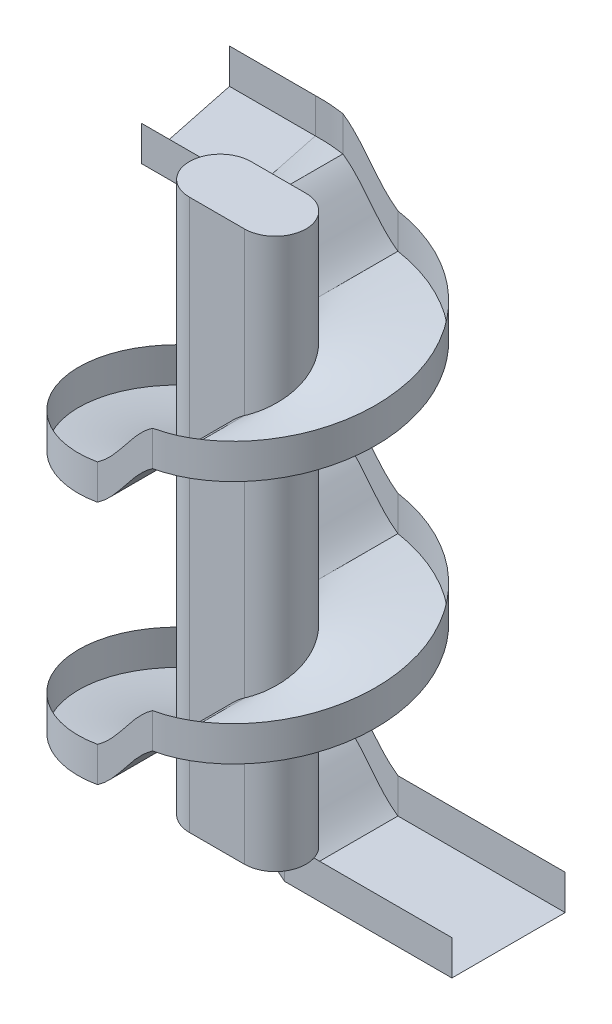
SolidWorks part; units mm, degrees
ref_plane "Front Plane" through (0, 0, 0) normal (0, 0, 1) x (1, 0, 0)
ref_plane "Top Plane" through (0, 0, 0) normal (0, 1, 0) x (1, 0, 0)
ref_plane "Right Plane" through (0, 0, 0) normal (1, 0, 0) x (0, 0, -1)
sketch "Sketch1" plane through (0, 0, 0) normal (0, 1, 0) x (1, 0, 0)
  line L0 (125, 0) -> (-125, 0) construction
  line L1 (125, -140) -> (-125, -140)
  line L2 (125, 140) -> (-125, 140)
  arc A0 (125, -140) -> (125, 140) centre (125, 0) ccw
  arc A1 (-125, 140) -> (-125, -140) centre (-125, 0) ccw
  point P2 (0, 0)
  dimension "D2" = 140
  dimension "D1" = 250
extrude "Boss-Extrude1" add sketch "Sketch1" along normal blind 2500
sketch "Sketch2" plane through (0, 0, 0) normal (0, 1, 0) x (1, 0, 0)
  line L0 (0, 0) -> (207.5125, 232.4141)
  point P3 (125, 140)
sketch "Sketch3" plane through (0, 0, 0) normal (0, 0, 1) x (1, 0, 0)
  line L0 (0, 0) -> (0, 2500)
  line L1 (-125, 2500) -> (125, 2500) construction
surface "Surface-Sweep1" parameters "D0"=810
sketch3d "3DSketch1"
  spline S2 degree 3 poles (215.4149, 2255.487, -593.0677) (166.0359, 1865.4917, -34.2644) (-1.7183, 1753.0109, 152.723) (-143.1351, 1653.9689, 138.8944) (-147.6117, 1650.8283, 138.2359) (-156.4867, 1644.5664, 136.4882) (-160.8853, 1641.4451, 135.3991) (-169.592, 1635.2055, 132.7863) (-173.9017, 1632.0894, 131.262) (-179.2125, 1628.1692, 129.0826) (-180.271, 1627.3841, 128.633) (-182.3803, 1625.8114, 127.706) (-183.4301, 1625.0246, 127.2291) (-186.5537, 1622.6708, 125.7634) (-188.6059, 1621.1073, 124.7378) (-194.6711, 1616.4304, 121.5191) (-198.593, 1613.3309, 119.184) (-206.1879, 1607.1521, 114.1459) (-209.8612, 1604.0737, 111.4426) (-216.9467, 1597.919, 105.6725) (-220.3543, 1594.8339, 102.6096) (-225.2526, 1590.1828, 97.7482) (-226.8498, 1588.6284, 96.0831) (-229.9709, 1585.5098, 92.6632) (-231.4853, 1583.9547, 90.9185) (-235.8841, 1579.3068, 85.5917) (-238.6272, 1576.2278, 81.9134) (-243.7356, 1570.0929, 74.3157) (-246.1013, 1567.0395, 70.3947) (-250.4404, 1560.9151, 62.3349) (-252.4149, 1557.8468, 58.1948) (-255.0755, 1553.2232, 51.8234) (-255.9121, 1551.6785, 49.6727) (-257.09, 1549.3547, 46.4066) (-257.4702, 1548.578, 45.3099) (-258.2023, 1547.027, 43.1101) (-258.5541, 1546.253, 42.0075) (-260.2425, 1542.3895, 36.4808) (-261.3671, 1539.3199, 32.0168) (-263.1715, 1533.2068, 23.0154) (-263.85, 1530.1546, 18.4837) (-264.761, 1524.0396, 9.3717) (-264.9936, 1520.9776, 4.7909) (-265.003, 1516.3659, -2.1103) (-264.9227, 1514.0555, -5.5684) (-264.7129, 1511.7358, -9.0364) (-264.5439, 1510.187, -11.3505) (-264.445, 1509.4119, -12.5078) (-263.8798, 1505.548, -18.2726) (-263.2012, 1502.4828, -22.8368) (-261.4079, 1496.3583, -31.843) (-260.2933, 1493.3005, -36.286) (-257.635, 1487.1786, -45.0432) (-256.0914, 1484.1145, -49.3574) (-253.4529, 1479.502, -55.7236) (-252.0528, 1477.1917, -58.8804) (-250.5303, 1474.873, -61.9959) (-249.4879, 1473.3251, -64.0634) (-248.9523, 1472.5492, -65.0935) (-246.2137, 1468.6752, -70.2051) (-243.8354, 1465.5946, -74.1565) (-238.7265, 1459.4405, -81.7761) (-235.9952, 1456.3692, -85.4455) (-230.1896, 1450.2225, -92.4987) (-227.1152, 1447.1472, -95.8826) (-222.2492, 1442.5197, -100.7365) (-220.5848, 1440.9748, -102.3174) (-217.1708, 1437.878, -105.4032) (-215.4213, 1436.3261, -106.9081) (-212.7356, 1433.9864, -109.1045) (-211.8308, 1433.2053, -109.8259) (-210.0089, 1431.6465, -111.2422) (-207.2547, 1429.3106, -113.3288) (-204.4379, 1426.9806, -115.3033) (-198.7238, 1422.3254, -119.1038) (-194.8073, 1419.2283, -121.4399) (-186.7723, 1413.0313, -125.7175) (-182.6539, 1409.9313, -127.659) (-176.3314, 1405.2672, -130.2701) (-174.1997, 1403.7102, -131.0901) (-169.8932, 1400.5825, -132.6267) (-167.7179, 1399.0126, -133.3433) (-164.4225, 1396.6471, -134.3398) (-163.3177, 1395.8562, -134.6591) (-161.1023, 1394.2739, -135.2699) (-157.7726, 1391.9015, -136.1439) (-154.4242, 1389.531, -136.892) (-147.7049, 1384.7891, -138.2221) (-143.1955, 1381.6269, -138.8873) (-10.2284, 1288.5955, -151.9254) (139.3738, 1193.9891, 12.7072) (-68.7291, 543.0017, 420.957) knots -0.917382 -0.917382 -0.917382 -0.917382 0.03125 0.03125 0.0625 0.0625 0.09375 0.09375 0.125 0.125 0.132813 0.132813 0.140625 0.140625 0.15625 0.15625 0.1875 0.1875 0.21875 0.21875 0.25 0.25 0.265625 0.265625 0.28125 0.28125 0.3125 0.3125 0.34375 0.34375 0.375 0.375 0.390625 0.390625 0.398438 0.398438 0.40625 0.40625 0.4375 0.4375 0.46875 0.46875 0.5 0.5 0.515625 0.523438 0.523438 0.53125 0.53125 0.5625 0.5625 0.59375 0.59375 0.625 0.625 0.640625 0.648438 0.648438 0.65625 0.65625 0.6875 0.6875 0.71875 0.71875 0.75 0.75 0.765625 0.765625 0.78125 0.78125 0.789063 0.789063 0.796875 0.8125 0.8125 0.84375 0.84375 0.875 0.875 0.890625 0.890625 0.90625 0.90625 0.914063 0.914063 0.921875 0.9375 0.9375 0.96875 0.96875 1.854106 1.854106 1.854106 1.854106 only from (-125, 1666.6667, 140) to (-125, 1368.8979, -140)
  spline S3 degree 3 poles (215.4149, 1144.3759, -593.0677) (166.0359, 754.3806, -34.2644) (-1.7183, 641.8998, 152.723) (-143.1351, 542.8578, 138.8944) (-147.6117, 539.7172, 138.2359) (-156.4867, 533.4553, 136.4882) (-160.8853, 530.334, 135.3991) (-169.592, 524.0944, 132.7863) (-173.9017, 520.9783, 131.262) (-179.2125, 517.0581, 129.0826) (-180.271, 516.273, 128.633) (-182.3803, 514.7003, 127.706) (-183.4301, 513.9134, 127.2291) (-186.5537, 511.5597, 125.7634) (-188.6059, 509.9961, 124.7378) (-194.6711, 505.3193, 121.5191) (-198.593, 502.2198, 119.184) (-206.1879, 496.041, 114.1459) (-209.8612, 492.9626, 111.4426) (-216.9467, 486.8079, 105.6725) (-220.3543, 483.7228, 102.6096) (-225.2526, 479.0716, 97.7482) (-226.8498, 477.5173, 96.0831) (-229.9709, 474.3987, 92.6632) (-231.4853, 472.8436, 90.9185) (-235.8841, 468.1957, 85.5917) (-238.6272, 465.1167, 81.9134) (-243.7356, 458.9818, 74.3157) (-246.1013, 455.9284, 70.3947) (-250.4404, 449.804, 62.3349) (-252.4149, 446.7357, 58.1948) (-255.0755, 442.1121, 51.8234) (-255.9121, 440.5674, 49.6727) (-257.09, 438.2436, 46.4066) (-257.4702, 437.4669, 45.3099) (-258.2023, 435.9159, 43.1101) (-258.5541, 435.1419, 42.0075) (-260.2425, 431.2784, 36.4808) (-261.3671, 428.2088, 32.0168) (-263.1715, 422.0957, 23.0154) (-263.85, 419.0435, 18.4837) (-264.761, 412.9285, 9.3717) (-264.9936, 409.8665, 4.7909) (-265.003, 405.2548, -2.1103) (-264.9227, 402.9444, -5.5684) (-264.7129, 400.6247, -9.0364) (-264.5439, 399.0759, -11.3505) (-264.445, 398.3008, -12.5078) (-263.8798, 394.4369, -18.2726) (-263.2012, 391.3717, -22.8368) (-261.4079, 385.2472, -31.843) (-260.2933, 382.1894, -36.286) (-257.635, 376.0674, -45.0432) (-256.0914, 373.0033, -49.3574) (-253.4529, 368.3909, -55.7236) (-252.0528, 366.0806, -58.8804) (-250.5303, 363.7619, -61.9959) (-249.4879, 362.214, -64.0634) (-248.9523, 361.4381, -65.0935) (-246.2137, 357.5641, -70.2051) (-243.8354, 354.4835, -74.1565) (-238.7265, 348.3294, -81.7761) (-235.9952, 345.258, -85.4455) (-230.1896, 339.1114, -92.4987) (-227.1152, 336.0361, -95.8826) (-222.2492, 331.4086, -100.7365) (-220.5848, 329.8637, -102.3174) (-217.1708, 326.7669, -105.4032) (-215.4213, 325.215, -106.9081) (-212.7356, 322.8753, -109.1045) (-211.8308, 322.0942, -109.8259) (-210.0089, 320.5354, -111.2422) (-207.2547, 318.1995, -113.3288) (-204.4379, 315.8695, -115.3033) (-198.7238, 311.2143, -119.1038) (-194.8073, 308.1172, -121.4399) (-186.7723, 301.9202, -125.7175) (-182.6539, 298.8202, -127.659) (-176.3314, 294.1561, -130.2701) (-174.1997, 292.5991, -131.0901) (-169.8932, 289.4714, -132.6267) (-167.7179, 287.9015, -133.3433) (-164.4225, 285.536, -134.3398) (-163.3177, 284.7451, -134.6591) (-161.1023, 283.1628, -135.2699) (-157.7726, 280.7904, -136.1439) (-154.4242, 278.4199, -136.892) (-147.7049, 273.678, -138.2221) (-143.1955, 270.5157, -138.8873) (-10.2284, 177.4843, -151.9254) (139.3738, 82.878, 12.7072) (-68.7291, -568.1094, 420.957) knots -0.917382 -0.917382 -0.917382 -0.917382 0.03125 0.03125 0.0625 0.0625 0.09375 0.09375 0.125 0.125 0.132813 0.132813 0.140625 0.140625 0.15625 0.15625 0.1875 0.1875 0.21875 0.21875 0.25 0.25 0.265625 0.265625 0.28125 0.28125 0.3125 0.3125 0.34375 0.34375 0.375 0.375 0.390625 0.390625 0.398438 0.398438 0.40625 0.40625 0.4375 0.4375 0.46875 0.46875 0.5 0.5 0.515625 0.523438 0.523438 0.53125 0.53125 0.5625 0.5625 0.59375 0.59375 0.625 0.625 0.640625 0.648438 0.648438 0.65625 0.65625 0.6875 0.6875 0.71875 0.71875 0.75 0.75 0.765625 0.765625 0.78125 0.78125 0.789063 0.789063 0.796875 0.8125 0.8125 0.84375 0.84375 0.875 0.875 0.890625 0.890625 0.90625 0.90625 0.914063 0.914063 0.921875 0.9375 0.9375 0.96875 0.96875 1.854106 1.854106 1.854106 1.854106 only from (-125, 555.5556, 140) to (-125, 257.7868, -140)
  spline S4 degree 3 poles (-167.7542, 1598.7248, 330.6483) (117.7392, 2309.6969, 1.7989) (-12.367, 2401.3101, -145.9603) (-134.5575, 2486.6957, -139.6938) (-136.9403, 2488.3611, -139.5104) (-284.7397, 2591.7937, -124.3152) (-410.6575, 2687.9461, 118.4195) (-310.3715, 3060.5098, 676.0833) knots -12.296716 -12.296716 -12.296716 -12.296716 0.25 0.25 0.5 0.5 15.791017 15.791017 15.791017 15.791017 only from (-125, 2480.009, -140) to (-153.5135, 2500, -137.0656)
  spline S5 degree 3 poles (-125, 2480.009, -140) (-127.392, 2481.6883, -140) (-129.7832, 2483.3595, -139.9387) (-134.5575, 2486.6957, -139.6938) (-136.9403, 2488.3611, -139.5104) (-144.073, 2493.3527, -138.7771) (-148.8073, 2496.6744, -138.0446) (-153.5135, 2500, -137.0656) knots 0 0 0 0 0.25 0.25 0.5 0.5 1 1 1 1
  spline S6 degree 3 poles (-125, 555.5556, 140) (-129.5716, 552.3516, 140) (-134.1151, 549.175, 139.7764) (-143.1351, 542.8578, 138.8944) (-147.6117, 539.7172, 138.2359) (-156.4867, 533.4553, 136.4882) (-160.8853, 530.334, 135.3991) (-169.592, 524.0944, 132.7863) (-173.9017, 520.9783, 131.262) (-179.2125, 517.0581, 129.0826) (-180.271, 516.273, 128.633) (-182.3803, 514.7003, 127.706) (-183.4301, 513.9134, 127.2291) (-186.5537, 511.5597, 125.7634) (-188.6059, 509.9961, 124.7378) (-194.6711, 505.3193, 121.5191) (-198.593, 502.2198, 119.184) (-206.1879, 496.041, 114.1459) (-209.8612, 492.9626, 111.4426) (-216.9467, 486.8079, 105.6725) (-220.3543, 483.7228, 102.6096) (-225.2526, 479.0716, 97.7482) (-226.8498, 477.5173, 96.0831) (-229.9709, 474.3987, 92.6632) (-231.4853, 472.8436, 90.9185) (-235.8841, 468.1957, 85.5917) (-238.6272, 465.1167, 81.9134) (-243.7356, 458.9818, 74.3157) (-246.1013, 455.9284, 70.3947) (-250.4404, 449.804, 62.3349) (-252.4149, 446.7357, 58.1948) (-255.0755, 442.1121, 51.8234) (-255.9121, 440.5674, 49.6727) (-257.09, 438.2436, 46.4066) (-257.4702, 437.4669, 45.3099) (-258.2023, 435.9159, 43.1101) (-258.5541, 435.1419, 42.0075) (-260.2425, 431.2784, 36.4808) (-261.3671, 428.2088, 32.0168) (-263.1715, 422.0957, 23.0154) (-263.85, 419.0435, 18.4837) (-264.761, 412.9285, 9.3717) (-264.9936, 409.8665, 4.7909) (-265.003, 405.2548, -2.1103) (-264.9227, 402.9444, -5.5684) (-264.7129, 400.6247, -9.0364) (-264.5439, 399.0759, -11.3505) (-264.445, 398.3008, -12.5078) (-263.8798, 394.4369, -18.2726) (-263.2012, 391.3717, -22.8368) (-261.4079, 385.2472, -31.843) (-260.2933, 382.1894, -36.286) (-257.635, 376.0674, -45.0432) (-256.0914, 373.0033, -49.3574) (-253.4529, 368.3909, -55.7236) (-252.0528, 366.0806, -58.8804) (-250.5303, 363.7619, -61.9959) (-249.4879, 362.214, -64.0634) (-248.9523, 361.4381, -65.0935) (-246.2137, 357.5641, -70.2051) (-243.8354, 354.4835, -74.1565) (-238.7265, 348.3294, -81.7761) (-235.9952, 345.258, -85.4455) (-230.1896, 339.1114, -92.4987) (-227.1152, 336.0361, -95.8826) (-222.2492, 331.4086, -100.7365) (-220.5848, 329.8637, -102.3174) (-217.1708, 326.7669, -105.4032) (-215.4213, 325.215, -106.9081) (-212.7356, 322.8753, -109.1045) (-211.8308, 322.0942, -109.8259) (-210.0089, 320.5354, -111.2422) (-207.2547, 318.1995, -113.3288) (-204.4379, 315.8695, -115.3033) (-198.7238, 311.2143, -119.1038) (-194.8073, 308.1172, -121.4399) (-186.7723, 301.9202, -125.7175) (-182.6539, 298.8202, -127.659) (-176.3314, 294.1561, -130.2701) (-174.1997, 292.5991, -131.0901) (-169.8932, 289.4714, -132.6267) (-167.7179, 287.9015, -133.3433) (-164.4225, 285.536, -134.3398) (-163.3177, 284.7451, -134.6591) (-161.1023, 283.1628, -135.2699) (-157.7726, 280.7904, -136.1439) (-154.4242, 278.4199, -136.892) (-147.7049, 273.678, -138.2221) (-143.1955, 270.5157, -138.8873) (-134.129, 264.1723, -139.7763) (-129.5694, 260.9946, -140) (-125, 257.7868, -140) knots 0 0 0 0 0.03125 0.03125 0.0625 0.0625 0.09375 0.09375 0.125 0.125 0.132813 0.132813 0.140625 0.140625 0.15625 0.15625 0.1875 0.1875 0.21875 0.21875 0.25 0.25 0.265625 0.265625 0.28125 0.28125 0.3125 0.3125 0.34375 0.34375 0.375 0.375 0.390625 0.390625 0.398438 0.398438 0.40625 0.40625 0.4375 0.4375 0.46875 0.46875 0.5 0.5 0.515625 0.523438 0.523438 0.53125 0.53125 0.5625 0.5625 0.59375 0.59375 0.625 0.625 0.640625 0.648438 0.648438 0.65625 0.65625 0.6875 0.6875 0.71875 0.71875 0.75 0.75 0.765625 0.765625 0.78125 0.78125 0.789063 0.789063 0.796875 0.8125 0.8125 0.84375 0.84375 0.875 0.875 0.890625 0.890625 0.90625 0.90625 0.914063 0.914063 0.921875 0.9375 0.9375 0.96875 0.96875 1 1 1 1
  spline S7 degree 3 poles (-125, 1666.6667, 140) (-129.5716, 1663.4627, 140) (-134.1151, 1660.2861, 139.7764) (-143.1351, 1653.9689, 138.8944) (-147.6117, 1650.8283, 138.2359) (-156.4867, 1644.5664, 136.4882) (-160.8853, 1641.4451, 135.3991) (-169.592, 1635.2055, 132.7863) (-173.9017, 1632.0894, 131.262) (-179.2125, 1628.1692, 129.0826) (-180.271, 1627.3841, 128.633) (-182.3803, 1625.8114, 127.706) (-183.4301, 1625.0246, 127.2291) (-186.5537, 1622.6708, 125.7634) (-188.6059, 1621.1073, 124.7378) (-194.6711, 1616.4304, 121.5191) (-198.593, 1613.3309, 119.184) (-206.1879, 1607.1521, 114.1459) (-209.8612, 1604.0737, 111.4426) (-216.9467, 1597.919, 105.6725) (-220.3543, 1594.8339, 102.6096) (-225.2526, 1590.1828, 97.7482) (-226.8498, 1588.6284, 96.0831) (-229.9709, 1585.5098, 92.6632) (-231.4853, 1583.9547, 90.9185) (-235.8841, 1579.3068, 85.5917) (-238.6272, 1576.2278, 81.9134) (-243.7356, 1570.0929, 74.3157) (-246.1013, 1567.0395, 70.3947) (-250.4404, 1560.9151, 62.3349) (-252.4149, 1557.8468, 58.1948) (-255.0755, 1553.2232, 51.8234) (-255.9121, 1551.6785, 49.6727) (-257.09, 1549.3547, 46.4066) (-257.4702, 1548.578, 45.3099) (-258.2023, 1547.027, 43.1101) (-258.5541, 1546.253, 42.0075) (-260.2425, 1542.3895, 36.4808) (-261.3671, 1539.3199, 32.0168) (-263.1715, 1533.2068, 23.0154) (-263.85, 1530.1546, 18.4837) (-264.761, 1524.0396, 9.3717) (-264.9936, 1520.9776, 4.7909) (-265.003, 1516.3659, -2.1103) (-264.9227, 1514.0555, -5.5684) (-264.7129, 1511.7358, -9.0364) (-264.5439, 1510.187, -11.3505) (-264.445, 1509.4119, -12.5078) (-263.8798, 1505.548, -18.2726) (-263.2012, 1502.4828, -22.8368) (-261.4079, 1496.3583, -31.843) (-260.2933, 1493.3005, -36.286) (-257.635, 1487.1786, -45.0432) (-256.0914, 1484.1145, -49.3574) (-253.4529, 1479.502, -55.7236) (-252.0528, 1477.1917, -58.8804) (-250.5303, 1474.873, -61.9959) (-249.4879, 1473.3251, -64.0634) (-248.9523, 1472.5492, -65.0935) (-246.2137, 1468.6752, -70.2051) (-243.8354, 1465.5946, -74.1565) (-238.7265, 1459.4405, -81.7761) (-235.9952, 1456.3692, -85.4455) (-230.1896, 1450.2225, -92.4987) (-227.1152, 1447.1472, -95.8826) (-222.2492, 1442.5197, -100.7365) (-220.5848, 1440.9748, -102.3174) (-217.1708, 1437.878, -105.4032) (-215.4213, 1436.3261, -106.9081) (-212.7356, 1433.9864, -109.1045) (-211.8308, 1433.2053, -109.8259) (-210.0089, 1431.6465, -111.2422) (-207.2547, 1429.3106, -113.3288) (-204.4379, 1426.9806, -115.3033) (-198.7238, 1422.3254, -119.1038) (-194.8073, 1419.2283, -121.4399) (-186.7723, 1413.0313, -125.7175) (-182.6539, 1409.9313, -127.659) (-176.3314, 1405.2672, -130.2701) (-174.1997, 1403.7102, -131.0901) (-169.8932, 1400.5825, -132.6267) (-167.7179, 1399.0126, -133.3433) (-164.4225, 1396.6471, -134.3398) (-163.3177, 1395.8562, -134.6591) (-161.1023, 1394.2739, -135.2699) (-157.7726, 1391.9015, -136.1439) (-154.4242, 1389.531, -136.892) (-147.7049, 1384.7891, -138.2221) (-143.1955, 1381.6269, -138.8873) (-134.129, 1375.2834, -139.7763) (-129.5694, 1372.1057, -140) (-125, 1368.8979, -140) knots 0 0 0 0 0.03125 0.03125 0.0625 0.0625 0.09375 0.09375 0.125 0.125 0.132813 0.132813 0.140625 0.140625 0.15625 0.15625 0.1875 0.1875 0.21875 0.21875 0.25 0.25 0.265625 0.265625 0.28125 0.28125 0.3125 0.3125 0.34375 0.34375 0.375 0.375 0.390625 0.390625 0.398438 0.398438 0.40625 0.40625 0.4375 0.4375 0.46875 0.46875 0.5 0.5 0.515625 0.523438 0.523438 0.53125 0.53125 0.5625 0.5625 0.59375 0.59375 0.625 0.625 0.640625 0.648438 0.648438 0.65625 0.65625 0.6875 0.6875 0.71875 0.71875 0.75 0.75 0.765625 0.765625 0.78125 0.78125 0.789063 0.789063 0.796875 0.8125 0.8125 0.84375 0.84375 0.875 0.875 0.890625 0.890625 0.90625 0.90625 0.914063 0.914063 0.921875 0.9375 0.9375 0.96875 0.96875 1 1 1 1
  spline S10 degree 3 poles (-125, 2480.009, -140) (-118.7718, 2475.6366, -140) (-112.7239, 2471.0883, -140) (-100.9507, 2461.6769, -140) (-95.2253, 2456.814, -140) (-86.8409, 2449.3207, -140) (-84.0831, 2446.7869, -140) (-78.6405, 2441.648, -140) (-75.9546, 2439.0439, -140) (-67.992, 2431.1392, -140) (-62.8102, 2425.7458, -140) (-55.1766, 2417.52, -140) (-52.6565, 2414.7542, -140) (-47.6686, 2409.1717, -140) (-45.1991, 2406.3566, -140) (-37.8498, 2397.8534, -140) (-33.0294, 2392.1073, -140) (-25.8606, 2383.4281, -140) (-23.4855, 2380.5209, -140) (-18.7597, 2374.6826, -140) (-14.0567, 2368.822, -140) (-9.3797, 2362.9361, -140) (-4.7059, 2357.0471, -140) (-2.3688, 2354.1027, -140) (4.6398, 2345.2672, -140) (9.3013, 2339.3663, -140) (16.3366, 2330.5565, -140) (18.6889, 2327.6267, -140) (23.4177, 2321.7907, -140) (25.7957, 2318.8859, -140) (32.9583, 2310.1988, -140) (37.7772, 2304.4496, -140) (45.1287, 2295.9447, -140) (47.5998, 2293.1295, -140) (52.5922, 2287.5477, -140) (55.1136, 2284.7811, -140) (62.7435, 2276.5446, -140) (67.9259, 2271.146, -140) (75.8942, 2263.2358, -140) (78.5828, 2260.6304, -140) (84.0327, 2255.4897, -140) (86.7948, 2252.9552, -140) (95.18, 2245.447, -140) (100.9093, 2240.5757, -140) (112.6976, 2231.1511, -140) (118.7566, 2226.5978, -140) (125, 2222.2222, -140) knots 0 0 0 0 0.0625 0.0625 0.125 0.125 0.15625 0.15625 0.1875 0.1875 0.25 0.25 0.28125 0.28125 0.3125 0.3125 0.375 0.375 0.40625 0.40625 0.4375 0.46875 0.46875 0.5 0.5 0.5625 0.5625 0.59375 0.59375 0.625 0.625 0.6875 0.6875 0.71875 0.71875 0.75 0.75 0.8125 0.8125 0.84375 0.84375 0.875 0.875 0.9375 0.9375 1 1 1 1
  spline S11 degree 3 poles (-125, 1368.8979, -140) (-118.7718, 1364.5255, -140) (-112.7239, 1359.9772, -140) (-100.9507, 1350.5658, -140) (-95.2253, 1345.7029, -140) (-86.8409, 1338.2096, -140) (-84.0831, 1335.6758, -140) (-78.6405, 1330.5369, -140) (-75.9546, 1327.9328, -140) (-67.992, 1320.0281, -140) (-62.8102, 1314.6347, -140) (-55.1766, 1306.4089, -140) (-52.6565, 1303.6431, -140) (-47.6686, 1298.0606, -140) (-45.1991, 1295.2455, -140) (-37.8498, 1286.7423, -140) (-33.0294, 1280.9962, -140) (-25.8606, 1272.317, -140) (-23.4855, 1269.4098, -140) (-18.7597, 1263.5715, -140) (-14.0567, 1257.7109, -140) (-9.3797, 1251.825, -140) (-4.7059, 1245.936, -140) (-2.3688, 1242.9916, -140) (4.6398, 1234.1561, -140) (9.3013, 1228.2552, -140) (16.3366, 1219.4453, -140) (18.6889, 1216.5156, -140) (23.4177, 1210.6796, -140) (25.7957, 1207.7747, -140) (32.9583, 1199.0876, -140) (37.7772, 1193.3385, -140) (45.1287, 1184.8336, -140) (47.5998, 1182.0184, -140) (52.5922, 1176.4366, -140) (55.1136, 1173.67, -140) (62.7435, 1165.4335, -140) (67.9259, 1160.0348, -140) (75.8942, 1152.1247, -140) (78.5828, 1149.5193, -140) (84.0327, 1144.3786, -140) (86.7948, 1141.8441, -140) (95.18, 1134.3359, -140) (100.9093, 1129.4646, -140) (112.6976, 1120.04, -140) (118.7566, 1115.4867, -140) (125, 1111.1111, -140) knots 0 0 0 0 0.0625 0.0625 0.125 0.125 0.15625 0.15625 0.1875 0.1875 0.25 0.25 0.28125 0.28125 0.3125 0.3125 0.375 0.375 0.40625 0.40625 0.4375 0.46875 0.46875 0.5 0.5 0.5625 0.5625 0.59375 0.59375 0.625 0.625 0.6875 0.6875 0.71875 0.71875 0.75 0.75 0.8125 0.8125 0.84375 0.84375 0.875 0.875 0.9375 0.9375 1 1 1 1
  spline S12 degree 3 poles (-125, 257.7868, -140) (-118.7718, 253.4144, -140) (-112.7239, 248.8661, -140) (-100.9507, 239.4547, -140) (-95.2253, 234.5918, -140) (-86.8409, 227.0985, -140) (-84.0831, 224.5647, -140) (-78.6405, 219.4258, -140) (-75.9546, 216.8217, -140) (-67.992, 208.9169, -140) (-62.8102, 203.5236, -140) (-55.1766, 195.2978, -140) (-52.6565, 192.532, -140) (-47.6686, 186.9494, -140) (-45.1991, 184.1343, -140) (-37.8498, 175.6312, -140) (-33.0294, 169.8851, -140) (-25.8606, 161.2059, -140) (-23.4855, 158.2987, -140) (-18.7597, 152.4604, -140) (-14.0567, 146.5998, -140) (-9.3797, 140.7139, -140) (-4.7059, 134.8249, -140) (-2.3688, 131.8805, -140) (4.6398, 123.045, -140) (9.3013, 117.1441, -140) (16.3366, 108.3342, -140) (18.6889, 105.4045, -140) (23.4177, 99.5685, -140) (25.7957, 96.6636, -140) (32.9583, 87.9765, -140) (37.7772, 82.2274, -140) (45.1287, 73.7225, -140) (47.5998, 70.9073, -140) (52.5922, 65.3255, -140) (55.1136, 62.5589, -140) (62.7435, 54.3224, -140) (67.9259, 48.9237, -140) (75.8942, 41.0136, -140) (78.5828, 38.4082, -140) (84.0327, 33.2675, -140) (86.7948, 30.7329, -140) (95.18, 23.2248, -140) (100.9093, 18.3535, -140) (112.6976, 8.9289, -140) (118.7566, 4.3756, -140) (125, 0, -140) knots 0 0 0 0 0.0625 0.0625 0.125 0.125 0.15625 0.15625 0.1875 0.1875 0.25 0.25 0.28125 0.28125 0.3125 0.3125 0.375 0.375 0.40625 0.40625 0.4375 0.46875 0.46875 0.5 0.5 0.5625 0.5625 0.59375 0.59375 0.625 0.625 0.6875 0.6875 0.71875 0.71875 0.75 0.75 0.8125 0.8125 0.84375 0.84375 0.875 0.875 0.9375 0.9375 1 1 1 1
  spline S13 degree 3 poles (125, 1924.4535, 140) (118.7712, 1920.0807, 140) (112.7228, 1915.5319, 140) (100.9485, 1906.1196, 140) (95.2226, 1901.2561, 140) (86.8375, 1893.7621, 140) (84.0795, 1891.228, 140) (78.6364, 1886.0885, 140) (75.9503, 1883.4842, 140) (67.9871, 1875.5786, 140) (62.8049, 1870.1846, 140) (55.1707, 1861.9579, 140) (52.6504, 1859.1919, 140) (47.6621, 1853.6087, 140) (45.1923, 1850.7933, 140) (37.8425, 1842.2892, 140) (33.0217, 1836.5425, 140) (25.8523, 1827.8624, 140) (23.477, 1824.9549, 140) (18.7508, 1819.116, 140) (14.0474, 1813.2548, 140) (9.37, 1807.3683, 140) (4.6957, 1801.4787, 140) (2.3584, 1798.534, 140) (-4.6508, 1789.6977, 140) (-9.312, 1783.7972, 140) (-16.3497, 1774.9846, 140) (-18.7033, 1772.0534, 140) (-23.4362, 1766.2124, 140) (-25.8173, 1763.304, 140) (-32.9909, 1754.604, 140) (-37.8202, 1748.8429, 140) (-45.1967, 1740.3112, 140) (-47.6776, 1737.4856, 140) (-52.694, 1731.8796, 140) (-55.2303, 1729.0979, 140) (-62.9013, 1720.8221, 140) (-68.1057, 1715.4059, 140) (-76.0942, 1707.485, 140) (-78.7873, 1704.8786, 140) (-84.2411, 1699.7412, 140) (-87.0022, 1697.2108, 140) (-95.3768, 1689.7216, 140) (-101.0883, 1684.8723, 140) (-112.8114, 1675.5093, 140) (-118.8231, 1670.9956, 140) (-125, 1666.6667, 140) knots 0 0 0 0 0.0625 0.0625 0.125 0.125 0.15625 0.15625 0.1875 0.1875 0.25 0.25 0.28125 0.28125 0.3125 0.3125 0.375 0.375 0.40625 0.40625 0.4375 0.46875 0.46875 0.5 0.5 0.5625 0.5625 0.59375 0.59375 0.625 0.625 0.6875 0.6875 0.71875 0.71875 0.75 0.75 0.8125 0.8125 0.84375 0.84375 0.875 0.875 0.9375 0.9375 1 1 1 1
  spline S14 degree 3 poles (125, 813.3424, 140) (118.7712, 808.9696, 140) (112.7228, 804.4208, 140) (100.9485, 795.0085, 140) (95.2226, 790.145, 140) (86.8375, 782.651, 140) (84.0795, 780.1168, 140) (78.6364, 774.9774, 140) (75.9503, 772.3731, 140) (67.9871, 764.4674, 140) (62.8049, 759.0735, 140) (55.1707, 750.8468, 140) (52.6504, 748.0808, 140) (47.6621, 742.4976, 140) (45.1923, 739.6822, 140) (37.8425, 731.1781, 140) (33.0217, 725.4314, 140) (25.8523, 716.7513, 140) (23.477, 713.8438, 140) (18.7508, 708.0049, 140) (14.0474, 702.1437, 140) (9.37, 696.2572, 140) (4.6957, 690.3676, 140) (2.3584, 687.4229, 140) (-4.6508, 678.5866, 140) (-9.312, 672.6861, 140) (-16.3497, 663.8735, 140) (-18.7033, 660.9422, 140) (-23.4362, 655.1012, 140) (-25.8173, 652.1929, 140) (-32.9909, 643.4929, 140) (-37.8202, 637.7318, 140) (-45.1967, 629.2001, 140) (-47.6776, 626.3745, 140) (-52.694, 620.7685, 140) (-55.2303, 617.9868, 140) (-62.9013, 609.711, 140) (-68.1057, 604.2947, 140) (-76.0942, 596.3739, 140) (-78.7873, 593.7675, 140) (-84.2411, 588.6301, 140) (-87.0022, 586.0997, 140) (-95.3768, 578.6105, 140) (-101.0883, 573.7612, 140) (-112.8114, 564.3982, 140) (-118.8231, 559.8845, 140) (-125, 555.5556, 140) knots 0 0 0 0 0.0625 0.0625 0.125 0.125 0.15625 0.15625 0.1875 0.1875 0.25 0.25 0.28125 0.28125 0.3125 0.3125 0.375 0.375 0.40625 0.40625 0.4375 0.46875 0.46875 0.5 0.5 0.5625 0.5625 0.59375 0.59375 0.625 0.625 0.6875 0.6875 0.71875 0.71875 0.75 0.75 0.8125 0.8125 0.84375 0.84375 0.875 0.875 0.9375 0.9375 1 1 1 1
  spline S18 degree 3 poles (-215.4149, 1699.9315, 593.0677) (-166.0359, 1309.9361, 34.2644) (1.7183, 1197.4553, -152.723) (143.1351, 1098.4133, -138.8944) (147.6117, 1095.2728, -138.2359) (156.4867, 1089.0109, -136.4882) (160.8853, 1085.8895, -135.3991) (169.592, 1079.6499, -132.7863) (173.9017, 1076.5339, -131.262) (179.2125, 1072.6136, -129.0826) (180.271, 1071.8285, -128.633) (182.3803, 1070.2558, -127.706) (183.4301, 1069.469, -127.2291) (186.5537, 1067.1152, -125.7634) (188.6059, 1065.5517, -124.7378) (194.6711, 1060.8749, -121.5191) (198.593, 1057.7753, -119.184) (206.1879, 1051.5966, -114.1459) (209.8612, 1048.5181, -111.4426) (216.9467, 1042.3634, -105.6725) (220.3543, 1039.2784, -102.6096) (225.2526, 1034.6272, -97.7482) (226.8498, 1033.0729, -96.0831) (229.9709, 1029.9542, -92.6632) (231.4853, 1028.3992, -90.9185) (235.8841, 1023.7512, -85.5917) (238.6272, 1020.6722, -81.9134) (243.7356, 1014.5373, -74.3157) (246.1013, 1011.484, -70.3947) (250.4404, 1005.3596, -62.3349) (252.4149, 1002.2912, -58.1948) (255.0755, 997.6677, -51.8234) (255.9121, 996.123, -49.6727) (257.09, 993.7991, -46.4066) (257.4702, 993.0225, -45.3099) (258.2023, 991.4715, -43.1101) (258.5541, 990.6975, -42.0075) (260.2425, 986.8339, -36.4808) (261.3671, 983.7643, -32.0168) (263.1715, 977.6512, -23.0154) (263.85, 974.5991, -18.4837) (264.761, 968.4841, -9.3717) (264.9936, 965.422, -4.7909) (265.003, 960.8104, 2.1103) (264.9227, 958.4999, 5.5684) (264.7129, 956.1802, 9.0364) (264.5439, 954.6314, 11.3505) (264.445, 953.8564, 12.5078) (263.8798, 949.9925, 18.2726) (263.2012, 946.9273, 22.8368) (261.4079, 940.8027, 31.843) (260.2933, 937.7449, 36.286) (257.635, 931.623, 45.0432) (256.0914, 928.5589, 49.3574) (253.4529, 923.9465, 55.7236) (252.0528, 921.6362, 58.8804) (250.5303, 919.3175, 61.9959) (249.4879, 917.7695, 64.0634) (248.9523, 916.9936, 65.0935) (246.2137, 913.1196, 70.2051) (243.8354, 910.039, 74.1565) (238.7265, 903.8849, 81.7761) (235.9952, 900.8136, 85.4455) (230.1896, 894.667, 92.4987) (227.1152, 891.5917, 95.8826) (222.2492, 886.9642, 100.7365) (220.5848, 885.4192, 102.3174) (217.1708, 882.3225, 105.4032) (215.4213, 880.7706, 106.9081) (212.7356, 878.4308, 109.1045) (211.8308, 877.6498, 109.8259) (210.0089, 876.0909, 111.2422) (207.2547, 873.755, 113.3288) (204.4379, 871.425, 115.3033) (198.7238, 866.7698, 119.1038) (194.8073, 863.6728, 121.4399) (186.7723, 857.4757, 125.7175) (182.6539, 854.3757, 127.659) (176.3314, 849.7117, 130.2701) (174.1997, 848.1547, 131.0901) (169.8932, 845.0269, 132.6267) (167.7179, 843.4571, 133.3433) (164.4225, 841.0916, 134.3398) (163.3177, 840.3006, 134.6591) (161.1023, 838.7184, 135.2699) (157.7726, 836.346, 136.1439) (154.4242, 833.9754, 136.892) (147.7049, 829.2335, 138.2221) (143.1955, 826.0713, 138.8873) (10.2284, 733.0399, 151.9254) (-139.3738, 638.4335, -12.7072) (68.7291, -12.5538, -420.957) knots -0.917382 -0.917382 -0.917382 -0.917382 0.03125 0.03125 0.0625 0.0625 0.09375 0.09375 0.125 0.125 0.132813 0.132813 0.140625 0.140625 0.15625 0.15625 0.1875 0.1875 0.21875 0.21875 0.25 0.25 0.265625 0.265625 0.28125 0.28125 0.3125 0.3125 0.34375 0.34375 0.375 0.375 0.390625 0.390625 0.398438 0.398438 0.40625 0.40625 0.4375 0.4375 0.46875 0.46875 0.5 0.5 0.515625 0.523438 0.523438 0.53125 0.53125 0.5625 0.5625 0.59375 0.59375 0.625 0.625 0.640625 0.648438 0.648438 0.65625 0.65625 0.6875 0.6875 0.71875 0.71875 0.75 0.75 0.765625 0.765625 0.78125 0.78125 0.789063 0.789063 0.796875 0.8125 0.8125 0.84375 0.84375 0.875 0.875 0.890625 0.890625 0.90625 0.90625 0.914063 0.914063 0.921875 0.9375 0.9375 0.96875 0.96875 1.854106 1.854106 1.854106 1.854106 only from (125, 1111.1111, -140) to (125, 813.3424, 140)
  spline S19 degree 3 poles (-215.4149, 2811.0426, 593.0677) (-166.0359, 2421.0472, 34.2644) (1.7183, 2308.5664, -152.723) (143.1351, 2209.5244, -138.8944) (147.6117, 2206.3839, -138.2359) (156.4867, 2200.122, -136.4882) (160.8853, 2197.0007, -135.3991) (169.592, 2190.761, -132.7863) (173.9017, 2187.645, -131.262) (179.2125, 2183.7247, -129.0826) (180.271, 2182.9396, -128.633) (182.3803, 2181.3669, -127.706) (183.4301, 2180.5801, -127.2291) (186.5537, 2178.2263, -125.7634) (188.6059, 2176.6628, -124.7378) (194.6711, 2171.986, -121.5191) (198.593, 2168.8864, -119.184) (206.1879, 2162.7077, -114.1459) (209.8612, 2159.6292, -111.4426) (216.9467, 2153.4745, -105.6725) (220.3543, 2150.3895, -102.6096) (225.2526, 2145.7383, -97.7482) (226.8498, 2144.184, -96.0831) (229.9709, 2141.0653, -92.6632) (231.4853, 2139.5103, -90.9185) (235.8841, 2134.8623, -85.5917) (238.6272, 2131.7833, -81.9134) (243.7356, 2125.6484, -74.3157) (246.1013, 2122.5951, -70.3947) (250.4404, 2116.4707, -62.3349) (252.4149, 2113.4023, -58.1948) (255.0755, 2108.7788, -51.8234) (255.9121, 2107.2341, -49.6727) (257.09, 2104.9102, -46.4066) (257.4702, 2104.1336, -45.3099) (258.2023, 2102.5826, -43.1101) (258.5541, 2101.8086, -42.0075) (260.2425, 2097.945, -36.4808) (261.3671, 2094.8754, -32.0168) (263.1715, 2088.7624, -23.0154) (263.85, 2085.7102, -18.4837) (264.761, 2079.5952, -9.3717) (264.9936, 2076.5331, -4.7909) (265.003, 2071.9215, 2.1103) (264.9227, 2069.611, 5.5684) (264.7129, 2067.2913, 9.0364) (264.5439, 2065.7425, 11.3505) (264.445, 2064.9675, 12.5078) (263.8798, 2061.1036, 18.2726) (263.2012, 2058.0384, 22.8368) (261.4079, 2051.9138, 31.843) (260.2933, 2048.856, 36.286) (257.635, 2042.7341, 45.0432) (256.0914, 2039.67, 49.3574) (253.4529, 2035.0576, 55.7236) (252.0528, 2032.7473, 58.8804) (250.5303, 2030.4286, 61.9959) (249.4879, 2028.8807, 64.0634) (248.9523, 2028.1048, 65.0935) (246.2137, 2024.2307, 70.2051) (243.8354, 2021.1501, 74.1565) (238.7265, 2014.996, 81.7761) (235.9952, 2011.9247, 85.4455) (230.1896, 2005.7781, 92.4987) (227.1152, 2002.7028, 95.8826) (222.2492, 1998.0753, 100.7365) (220.5848, 1996.5303, 102.3174) (217.1708, 1993.4336, 105.4032) (215.4213, 1991.8817, 106.9081) (212.7356, 1989.5419, 109.1045) (211.8308, 1988.7609, 109.8259) (210.0089, 1987.202, 111.2422) (207.2547, 1984.8661, 113.3288) (204.4379, 1982.5361, 115.3033) (198.7238, 1977.8809, 119.1038) (194.8073, 1974.7839, 121.4399) (186.7723, 1968.5868, 125.7175) (182.6539, 1965.4868, 127.659) (176.3314, 1960.8228, 130.2701) (174.1997, 1959.2658, 131.0901) (169.8932, 1956.138, 132.6267) (167.7179, 1954.5682, 133.3433) (164.4225, 1952.2027, 134.3398) (163.3177, 1951.4117, 134.6591) (161.1023, 1949.8295, 135.2699) (157.7726, 1947.4571, 136.1439) (154.4242, 1945.0865, 136.892) (147.7049, 1940.3447, 138.2221) (143.1955, 1937.1824, 138.8873) (10.2284, 1844.151, 151.9254) (-139.3738, 1749.5446, -12.7072) (68.7291, 1098.5573, -420.957) knots -0.917382 -0.917382 -0.917382 -0.917382 0.03125 0.03125 0.0625 0.0625 0.09375 0.09375 0.125 0.125 0.132813 0.132813 0.140625 0.140625 0.15625 0.15625 0.1875 0.1875 0.21875 0.21875 0.25 0.25 0.265625 0.265625 0.28125 0.28125 0.3125 0.3125 0.34375 0.34375 0.375 0.375 0.390625 0.390625 0.398438 0.398438 0.40625 0.40625 0.4375 0.4375 0.46875 0.46875 0.5 0.5 0.515625 0.523438 0.523438 0.53125 0.53125 0.5625 0.5625 0.59375 0.59375 0.625 0.625 0.640625 0.648438 0.648438 0.65625 0.65625 0.6875 0.6875 0.71875 0.71875 0.75 0.75 0.765625 0.765625 0.78125 0.78125 0.789063 0.789063 0.796875 0.8125 0.8125 0.84375 0.84375 0.875 0.875 0.890625 0.890625 0.90625 0.90625 0.914063 0.914063 0.921875 0.9375 0.9375 0.96875 0.96875 1.854106 1.854106 1.854106 1.854106 only from (125, 2222.2222, -140) to (125, 1924.4535, 140)
  spline S20 degree 3 poles (125, 2222.2222, -140) (129.5716, 2219.0183, -140) (134.1151, 2215.8417, -139.7764) (143.1351, 2209.5244, -138.8944) (147.6117, 2206.3839, -138.2359) (156.4867, 2200.122, -136.4882) (160.8853, 2197.0007, -135.3991) (169.592, 2190.761, -132.7863) (173.9017, 2187.645, -131.262) (179.2125, 2183.7247, -129.0826) (180.271, 2182.9396, -128.633) (182.3803, 2181.3669, -127.706) (183.4301, 2180.5801, -127.2291) (186.5537, 2178.2263, -125.7634) (188.6059, 2176.6628, -124.7378) (194.6711, 2171.986, -121.5191) (198.593, 2168.8864, -119.184) (206.1879, 2162.7077, -114.1459) (209.8612, 2159.6292, -111.4426) (216.9467, 2153.4745, -105.6725) (220.3543, 2150.3895, -102.6096) (225.2526, 2145.7383, -97.7482) (226.8498, 2144.184, -96.0831) (229.9709, 2141.0653, -92.6632) (231.4853, 2139.5103, -90.9185) (235.8841, 2134.8623, -85.5917) (238.6272, 2131.7833, -81.9134) (243.7356, 2125.6484, -74.3157) (246.1013, 2122.5951, -70.3947) (250.4404, 2116.4707, -62.3349) (252.4149, 2113.4023, -58.1948) (255.0755, 2108.7788, -51.8234) (255.9121, 2107.2341, -49.6727) (257.09, 2104.9102, -46.4066) (257.4702, 2104.1336, -45.3099) (258.2023, 2102.5826, -43.1101) (258.5541, 2101.8086, -42.0075) (260.2425, 2097.945, -36.4808) (261.3671, 2094.8754, -32.0168) (263.1715, 2088.7624, -23.0154) (263.85, 2085.7102, -18.4837) (264.761, 2079.5952, -9.3717) (264.9936, 2076.5331, -4.7909) (265.003, 2071.9215, 2.1103) (264.9227, 2069.611, 5.5684) (264.7129, 2067.2913, 9.0364) (264.5439, 2065.7425, 11.3505) (264.445, 2064.9675, 12.5078) (263.8798, 2061.1036, 18.2726) (263.2012, 2058.0384, 22.8368) (261.4079, 2051.9138, 31.843) (260.2933, 2048.856, 36.286) (257.635, 2042.7341, 45.0432) (256.0914, 2039.67, 49.3574) (253.4529, 2035.0576, 55.7236) (252.0528, 2032.7473, 58.8804) (250.5303, 2030.4286, 61.9959) (249.4879, 2028.8807, 64.0634) (248.9523, 2028.1048, 65.0935) (246.2137, 2024.2307, 70.2051) (243.8354, 2021.1501, 74.1565) (238.7265, 2014.996, 81.7761) (235.9952, 2011.9247, 85.4455) (230.1896, 2005.7781, 92.4987) (227.1152, 2002.7028, 95.8826) (222.2492, 1998.0753, 100.7365) (220.5848, 1996.5303, 102.3174) (217.1708, 1993.4336, 105.4032) (215.4213, 1991.8817, 106.9081) (212.7356, 1989.5419, 109.1045) (211.8308, 1988.7609, 109.8259) (210.0089, 1987.202, 111.2422) (207.2547, 1984.8661, 113.3288) (204.4379, 1982.5361, 115.3033) (198.7238, 1977.8809, 119.1038) (194.8073, 1974.7839, 121.4399) (186.7723, 1968.5868, 125.7175) (182.6539, 1965.4868, 127.659) (176.3314, 1960.8228, 130.2701) (174.1997, 1959.2658, 131.0901) (169.8932, 1956.138, 132.6267) (167.7179, 1954.5682, 133.3433) (164.4225, 1952.2027, 134.3398) (163.3177, 1951.4117, 134.6591) (161.1023, 1949.8295, 135.2699) (157.7726, 1947.4571, 136.1439) (154.4242, 1945.0865, 136.892) (147.7049, 1940.3447, 138.2221) (143.1955, 1937.1824, 138.8873) (134.129, 1930.8389, 139.7763) (129.5694, 1927.6613, 140) (125, 1924.4535, 140) knots 0 0 0 0 0.03125 0.03125 0.0625 0.0625 0.09375 0.09375 0.125 0.125 0.132813 0.132813 0.140625 0.140625 0.15625 0.15625 0.1875 0.1875 0.21875 0.21875 0.25 0.25 0.265625 0.265625 0.28125 0.28125 0.3125 0.3125 0.34375 0.34375 0.375 0.375 0.390625 0.390625 0.398438 0.398438 0.40625 0.40625 0.4375 0.4375 0.46875 0.46875 0.5 0.5 0.515625 0.523438 0.523438 0.53125 0.53125 0.5625 0.5625 0.59375 0.59375 0.625 0.625 0.640625 0.648438 0.648438 0.65625 0.65625 0.6875 0.6875 0.71875 0.71875 0.75 0.75 0.765625 0.765625 0.78125 0.78125 0.789063 0.789063 0.796875 0.8125 0.8125 0.84375 0.84375 0.875 0.875 0.890625 0.890625 0.90625 0.90625 0.914063 0.914063 0.921875 0.9375 0.9375 0.96875 0.96875 1 1 1 1
  spline S21 degree 3 poles (125, 1111.1111, -140) (129.5716, 1107.9072, -140) (134.1151, 1104.7305, -139.7764) (143.1351, 1098.4133, -138.8944) (147.6117, 1095.2728, -138.2359) (156.4867, 1089.0109, -136.4882) (160.8853, 1085.8895, -135.3991) (169.592, 1079.6499, -132.7863) (173.9017, 1076.5339, -131.262) (179.2125, 1072.6136, -129.0826) (180.271, 1071.8285, -128.633) (182.3803, 1070.2558, -127.706) (183.4301, 1069.469, -127.2291) (186.5537, 1067.1152, -125.7634) (188.6059, 1065.5517, -124.7378) (194.6711, 1060.8749, -121.5191) (198.593, 1057.7753, -119.184) (206.1879, 1051.5966, -114.1459) (209.8612, 1048.5181, -111.4426) (216.9467, 1042.3634, -105.6725) (220.3543, 1039.2784, -102.6096) (225.2526, 1034.6272, -97.7482) (226.8498, 1033.0729, -96.0831) (229.9709, 1029.9542, -92.6632) (231.4853, 1028.3992, -90.9185) (235.8841, 1023.7512, -85.5917) (238.6272, 1020.6722, -81.9134) (243.7356, 1014.5373, -74.3157) (246.1013, 1011.484, -70.3947) (250.4404, 1005.3596, -62.3349) (252.4149, 1002.2912, -58.1948) (255.0755, 997.6677, -51.8234) (255.9121, 996.123, -49.6727) (257.09, 993.7991, -46.4066) (257.4702, 993.0225, -45.3099) (258.2023, 991.4715, -43.1101) (258.5541, 990.6975, -42.0075) (260.2425, 986.8339, -36.4808) (261.3671, 983.7643, -32.0168) (263.1715, 977.6512, -23.0154) (263.85, 974.5991, -18.4837) (264.761, 968.4841, -9.3717) (264.9936, 965.422, -4.7909) (265.003, 960.8104, 2.1103) (264.9227, 958.4999, 5.5684) (264.7129, 956.1802, 9.0364) (264.5439, 954.6314, 11.3505) (264.445, 953.8564, 12.5078) (263.8798, 949.9925, 18.2726) (263.2012, 946.9273, 22.8368) (261.4079, 940.8027, 31.843) (260.2933, 937.7449, 36.286) (257.635, 931.623, 45.0432) (256.0914, 928.5589, 49.3574) (253.4529, 923.9465, 55.7236) (252.0528, 921.6362, 58.8804) (250.5303, 919.3175, 61.9959) (249.4879, 917.7695, 64.0634) (248.9523, 916.9936, 65.0935) (246.2137, 913.1196, 70.2051) (243.8354, 910.039, 74.1565) (238.7265, 903.8849, 81.7761) (235.9952, 900.8136, 85.4455) (230.1896, 894.667, 92.4987) (227.1152, 891.5917, 95.8826) (222.2492, 886.9642, 100.7365) (220.5848, 885.4192, 102.3174) (217.1708, 882.3225, 105.4032) (215.4213, 880.7706, 106.9081) (212.7356, 878.4308, 109.1045) (211.8308, 877.6498, 109.8259) (210.0089, 876.0909, 111.2422) (207.2547, 873.755, 113.3288) (204.4379, 871.425, 115.3033) (198.7238, 866.7698, 119.1038) (194.8073, 863.6728, 121.4399) (186.7723, 857.4757, 125.7175) (182.6539, 854.3757, 127.659) (176.3314, 849.7117, 130.2701) (174.1997, 848.1547, 131.0901) (169.8932, 845.0269, 132.6267) (167.7179, 843.4571, 133.3433) (164.4225, 841.0916, 134.3398) (163.3177, 840.3006, 134.6591) (161.1023, 838.7184, 135.2699) (157.7726, 836.346, 136.1439) (154.4242, 833.9754, 136.892) (147.7049, 829.2335, 138.2221) (143.1955, 826.0713, 138.8873) (134.129, 819.7278, 139.7763) (129.5694, 816.5502, 140) (125, 813.3424, 140) knots 0 0 0 0 0.03125 0.03125 0.0625 0.0625 0.09375 0.09375 0.125 0.125 0.132813 0.132813 0.140625 0.140625 0.15625 0.15625 0.1875 0.1875 0.21875 0.21875 0.25 0.25 0.265625 0.265625 0.28125 0.28125 0.3125 0.3125 0.34375 0.34375 0.375 0.375 0.390625 0.390625 0.398438 0.398438 0.40625 0.40625 0.4375 0.4375 0.46875 0.46875 0.5 0.5 0.515625 0.523438 0.523438 0.53125 0.53125 0.5625 0.5625 0.59375 0.59375 0.625 0.625 0.640625 0.648438 0.648438 0.65625 0.65625 0.6875 0.6875 0.71875 0.71875 0.75 0.75 0.765625 0.765625 0.78125 0.78125 0.789063 0.789063 0.796875 0.8125 0.8125 0.84375 0.84375 0.875 0.875 0.890625 0.890625 0.90625 0.90625 0.914063 0.914063 0.921875 0.9375 0.9375 0.96875 0.96875 1 1 1 1
  spline S25 degree 3 poles (-1100.666, 38.5548, -140) (-489.6107, 380.0719, -140) (-250.3187, 358.8576, -140) (-100.9507, 239.4547, -140) (-95.2253, 234.5918, -140) (-86.8409, 227.0985, -140) (-84.0831, 224.5647, -140) (-78.6405, 219.4258, -140) (-75.9546, 216.8217, -140) (-67.992, 208.9169, -140) (-62.8102, 203.5236, -140) (-55.1766, 195.2978, -140) (-52.6565, 192.532, -140) (-47.6686, 186.9494, -140) (-45.1991, 184.1343, -140) (-37.8498, 175.6312, -140) (-33.0294, 169.8851, -140) (-25.8606, 161.2059, -140) (-23.4855, 158.2987, -140) (-18.7597, 152.4604, -140) (-14.0567, 146.5998, -140) (-9.3797, 140.7139, -140) (-4.7059, 134.8249, -140) (-2.3688, 131.8805, -140) (4.6398, 123.045, -140) (9.3013, 117.1441, -140) (16.3366, 108.3342, -140) (18.6889, 105.4045, -140) (23.4177, 99.5685, -140) (25.7957, 96.6636, -140) (32.9583, 87.9765, -140) (37.7772, 82.2274, -140) (45.1287, 73.7225, -140) (47.5998, 70.9073, -140) (52.5922, 65.3255, -140) (55.1136, 62.5589, -140) (62.7435, 54.3224, -140) (67.9259, 48.9237, -140) (75.8942, 41.0136, -140) (78.5828, 38.4082, -140) (84.0327, 33.2675, -140) (86.7948, 30.7329, -140) (95.18, 23.2248, -140) (100.9093, 18.3535, -140) (249.5912, -100.5165, -140) (489.1648, -121.3481, -140) (1101.1691, 216.9379, -140) knots -1.460886 -1.460886 -1.460886 -1.460886 0.0625 0.0625 0.125 0.125 0.15625 0.15625 0.1875 0.1875 0.25 0.25 0.28125 0.28125 0.3125 0.3125 0.375 0.375 0.40625 0.40625 0.4375 0.46875 0.46875 0.5 0.5 0.5625 0.5625 0.59375 0.59375 0.625 0.625 0.6875 0.6875 0.71875 0.71875 0.75 0.75 0.8125 0.8125 0.84375 0.84375 0.875 0.875 0.9375 0.9375 2.451585 2.451585 2.451585 2.451585 only from (-125, 257.7868, -140) to (125, 0, -140)
  spline S26 degree 3 poles (-1100.666, 1149.6659, -140) (-489.6107, 1491.183, -140) (-250.3187, 1469.9687, -140) (-100.9507, 1350.5658, -140) (-95.2253, 1345.7029, -140) (-86.8409, 1338.2096, -140) (-84.0831, 1335.6758, -140) (-78.6405, 1330.5369, -140) (-75.9546, 1327.9328, -140) (-67.992, 1320.0281, -140) (-62.8102, 1314.6347, -140) (-55.1766, 1306.4089, -140) (-52.6565, 1303.6431, -140) (-47.6686, 1298.0606, -140) (-45.1991, 1295.2455, -140) (-37.8498, 1286.7423, -140) (-33.0294, 1280.9962, -140) (-25.8606, 1272.317, -140) (-23.4855, 1269.4098, -140) (-18.7597, 1263.5715, -140) (-14.0567, 1257.7109, -140) (-9.3797, 1251.825, -140) (-4.7059, 1245.936, -140) (-2.3688, 1242.9916, -140) (4.6398, 1234.1561, -140) (9.3013, 1228.2552, -140) (16.3366, 1219.4453, -140) (18.6889, 1216.5156, -140) (23.4177, 1210.6796, -140) (25.7957, 1207.7747, -140) (32.9583, 1199.0876, -140) (37.7772, 1193.3385, -140) (45.1287, 1184.8336, -140) (47.5998, 1182.0184, -140) (52.5922, 1176.4366, -140) (55.1136, 1173.67, -140) (62.7435, 1165.4335, -140) (67.9259, 1160.0348, -140) (75.8942, 1152.1247, -140) (78.5828, 1149.5193, -140) (84.0327, 1144.3786, -140) (86.7948, 1141.8441, -140) (95.18, 1134.3359, -140) (100.9093, 1129.4646, -140) (249.5912, 1010.5946, -140) (489.1648, 989.763, -140) (1101.1691, 1328.049, -140) knots -1.460886 -1.460886 -1.460886 -1.460886 0.0625 0.0625 0.125 0.125 0.15625 0.15625 0.1875 0.1875 0.25 0.25 0.28125 0.28125 0.3125 0.3125 0.375 0.375 0.40625 0.40625 0.4375 0.46875 0.46875 0.5 0.5 0.5625 0.5625 0.59375 0.59375 0.625 0.625 0.6875 0.6875 0.71875 0.71875 0.75 0.75 0.8125 0.8125 0.84375 0.84375 0.875 0.875 0.9375 0.9375 2.451585 2.451585 2.451585 2.451585 only from (-125, 1368.8979, -140) to (125, 1111.1111, -140)
  spline S27 degree 3 poles (-1100.666, 2260.777, -140) (-489.6107, 2602.2941, -140) (-250.3187, 2581.0798, -140) (-100.9507, 2461.6769, -140) (-95.2253, 2456.814, -140) (-86.8409, 2449.3207, -140) (-84.0831, 2446.7869, -140) (-78.6405, 2441.648, -140) (-75.9546, 2439.0439, -140) (-67.992, 2431.1392, -140) (-62.8102, 2425.7458, -140) (-55.1766, 2417.52, -140) (-52.6565, 2414.7542, -140) (-47.6686, 2409.1717, -140) (-45.1991, 2406.3566, -140) (-37.8498, 2397.8534, -140) (-33.0294, 2392.1073, -140) (-25.8606, 2383.4281, -140) (-23.4855, 2380.5209, -140) (-18.7597, 2374.6826, -140) (-14.0567, 2368.822, -140) (-9.3797, 2362.9361, -140) (-4.7059, 2357.0471, -140) (-2.3688, 2354.1027, -140) (4.6398, 2345.2672, -140) (9.3013, 2339.3663, -140) (16.3366, 2330.5565, -140) (18.6889, 2327.6267, -140) (23.4177, 2321.7907, -140) (25.7957, 2318.8859, -140) (32.9583, 2310.1988, -140) (37.7772, 2304.4496, -140) (45.1287, 2295.9447, -140) (47.5998, 2293.1295, -140) (52.5922, 2287.5477, -140) (55.1136, 2284.7811, -140) (62.7435, 2276.5446, -140) (67.9259, 2271.146, -140) (75.8942, 2263.2358, -140) (78.5828, 2260.6304, -140) (84.0327, 2255.4897, -140) (86.7948, 2252.9552, -140) (95.18, 2245.447, -140) (100.9093, 2240.5757, -140) (249.5912, 2121.7057, -140) (489.1648, 2100.8741, -140) (1101.1691, 2439.1601, -140) knots -1.460886 -1.460886 -1.460886 -1.460886 0.0625 0.0625 0.125 0.125 0.15625 0.15625 0.1875 0.1875 0.25 0.25 0.28125 0.28125 0.3125 0.3125 0.375 0.375 0.40625 0.40625 0.4375 0.46875 0.46875 0.5 0.5 0.5625 0.5625 0.59375 0.59375 0.625 0.625 0.6875 0.6875 0.71875 0.71875 0.75 0.75 0.8125 0.8125 0.84375 0.84375 0.875 0.875 0.9375 0.9375 2.451585 2.451585 2.451585 2.451585 only from (-125, 2480.009, -140) to (125, 2222.2222, -140)
  spline S28 degree 3 poles (1100.669, 594.1069, 140) (489.6079, 935.6288, 140) (250.3168, 914.4129, 140) (100.9485, 795.0085, 140) (95.2226, 790.145, 140) (86.8375, 782.651, 140) (84.0795, 780.1168, 140) (78.6364, 774.9774, 140) (75.9503, 772.3731, 140) (67.9871, 764.4674, 140) (62.8049, 759.0735, 140) (55.1707, 750.8468, 140) (52.6504, 748.0808, 140) (47.6621, 742.4976, 140) (45.1923, 739.6822, 140) (37.8425, 731.1781, 140) (33.0217, 725.4314, 140) (25.8523, 716.7513, 140) (23.477, 713.8438, 140) (18.7508, 708.0049, 140) (14.0474, 702.1437, 140) (9.37, 696.2572, 140) (4.6957, 690.3676, 140) (2.3584, 687.4229, 140) (-4.6508, 678.5866, 140) (-9.312, 672.6861, 140) (-16.3497, 663.8735, 140) (-18.7033, 660.9422, 140) (-23.4362, 655.1012, 140) (-25.8173, 652.1929, 140) (-32.9909, 643.4929, 140) (-37.8202, 637.7318, 140) (-45.1967, 629.2001, 140) (-47.6776, 626.3745, 140) (-52.694, 620.7685, 140) (-55.2303, 617.9868, 140) (-62.9013, 609.711, 140) (-68.1057, 604.2947, 140) (-76.0942, 596.3739, 140) (-78.7873, 593.7675, 140) (-84.2411, 588.6301, 140) (-87.0022, 586.0997, 140) (-95.3768, 578.6105, 140) (-101.0883, 573.7612, 140) (-255.7895, 450.2049, 140) (-501.4171, 439.5322, 140) (-1091.1414, 813.5351, 140) knots -1.460747 -1.460747 -1.460747 -1.460747 0.0625 0.0625 0.125 0.125 0.15625 0.15625 0.1875 0.1875 0.25 0.25 0.28125 0.28125 0.3125 0.3125 0.375 0.375 0.40625 0.40625 0.4375 0.46875 0.46875 0.5 0.5 0.5625 0.5625 0.59375 0.59375 0.625 0.625 0.6875 0.6875 0.71875 0.71875 0.75 0.75 0.8125 0.8125 0.84375 0.84375 0.875 0.875 0.9375 0.9375 2.524531 2.524531 2.524531 2.524531 only from (125, 813.3424, 140) to (-125, 555.5556, 140)
  spline S29 degree 3 poles (1100.669, 1705.218, 140) (489.6079, 2046.7399, 140) (250.3168, 2025.524, 140) (100.9485, 1906.1196, 140) (95.2226, 1901.2561, 140) (86.8375, 1893.7621, 140) (84.0795, 1891.228, 140) (78.6364, 1886.0885, 140) (75.9503, 1883.4842, 140) (67.9871, 1875.5786, 140) (62.8049, 1870.1846, 140) (55.1707, 1861.9579, 140) (52.6504, 1859.1919, 140) (47.6621, 1853.6087, 140) (45.1923, 1850.7933, 140) (37.8425, 1842.2892, 140) (33.0217, 1836.5425, 140) (25.8523, 1827.8624, 140) (23.477, 1824.9549, 140) (18.7508, 1819.116, 140) (14.0474, 1813.2548, 140) (9.37, 1807.3683, 140) (4.6957, 1801.4787, 140) (2.3584, 1798.534, 140) (-4.6508, 1789.6977, 140) (-9.312, 1783.7972, 140) (-16.3497, 1774.9846, 140) (-18.7033, 1772.0534, 140) (-23.4362, 1766.2124, 140) (-25.8173, 1763.304, 140) (-32.9909, 1754.604, 140) (-37.8202, 1748.8429, 140) (-45.1967, 1740.3112, 140) (-47.6776, 1737.4856, 140) (-52.694, 1731.8796, 140) (-55.2303, 1729.0979, 140) (-62.9013, 1720.8221, 140) (-68.1057, 1715.4059, 140) (-76.0942, 1707.485, 140) (-78.7873, 1704.8786, 140) (-84.2411, 1699.7412, 140) (-87.0022, 1697.2108, 140) (-95.3768, 1689.7216, 140) (-101.0883, 1684.8723, 140) (-255.7895, 1561.316, 140) (-501.4171, 1550.6433, 140) (-1091.1414, 1924.6462, 140) knots -1.460747 -1.460747 -1.460747 -1.460747 0.0625 0.0625 0.125 0.125 0.15625 0.15625 0.1875 0.1875 0.25 0.25 0.28125 0.28125 0.3125 0.3125 0.375 0.375 0.40625 0.40625 0.4375 0.46875 0.46875 0.5 0.5 0.5625 0.5625 0.59375 0.59375 0.625 0.625 0.6875 0.6875 0.71875 0.71875 0.75 0.75 0.8125 0.8125 0.84375 0.84375 0.875 0.875 0.9375 0.9375 2.524531 2.524531 2.524531 2.524531 only from (125, 1924.4535, 140) to (-125, 1666.6667, 140)
sketch "Sketch4" plane through (0, 0, 0) normal (1, 0, 0) x (0, 0, -1)
  line L2 (42.6486, 128.8942) -> (42.6486, -29.9206)
  line L3 (42.6486, -29.9206) -> (557.3514, -29.9206)
  line L4 (557.3514, 128.8942) -> (557.3514, -29.9206)
  point P0 (140, 128.8942)
surface "Surface-Sweep2"
other "Ruled Surface1" parameters "D1"=390, "D2"=3
other "Ruled Surface2" parameters "D1"=760, "D2"=3
